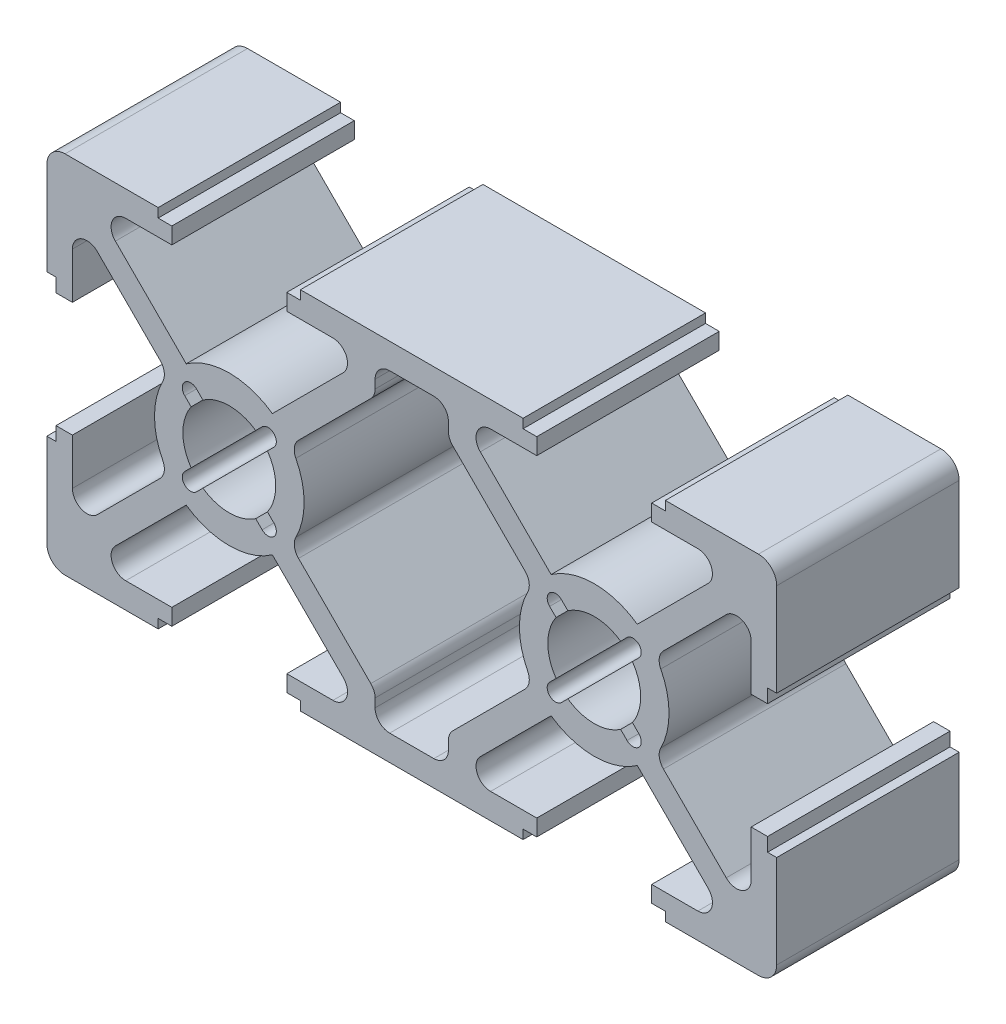
SolidWorks part; units mm, degrees
material "6063-T6"
ref_plane "Ön Düzlem" through (0, 0, 0) normal (0, 0, 1) x (1, 0, 0)
ref_plane "Üst Düzlem" through (0, 0, 0) normal (0, 1, 0) x (1, 0, 0)
ref_plane "Sağ Düzlem" through (0, 0, 0) normal (1, 0, 0) x (0, 0, -1)
sketch "Çizim3" plane through (0, 0, 0) normal (0, 0, 1) x (1, 0, 0)
  line L0 (20, 20) -> (20, 0) construction
  line L1 (0, 0) -> (40, 0) construction
  line L2 (1, 0) -> (6.1, 0)
  line L3 (0, 20) -> (40, 20) construction
  line L4 (40, 0) -> (40, 20) construction
  line L5 (26.1, 0) -> (26.1, 0.5)
  line L6 (0, 0) -> (20, 20) construction
  line L7 (20, 20) -> (40, 0) construction
  line L8 (0, 20) -> (20, 0) construction
  line L9 (20, 0) -> (40, 20) construction
  line L10 (0, 6.1) -> (0.5, 6.1)
  line L11 (0.5, 6.1) -> (0.5, 6.85)
  line L12 (0.5, 6.85) -> (1.4, 6.85)
  line L13 (1.4, 6.85) -> (1.4, 4.3213)
  line L14 (4.3213, 1.4) -> (6.85, 1.4)
  line L15 (6.85, 1.4) -> (6.85, 0.5)
  line L16 (6.85, 0.5) -> (6.1, 0.5)
  line L17 (6.1, 0.5) -> (6.1, 0)
  line L18 (0, 20) -> (0, 0) construction
  line L19 (0, 1) -> (0, 6.1)
  line L20 (6.85, 18.6) -> (6.85, 19.5)
  line L21 (6.85, 19.5) -> (6.1, 19.5)
  line L22 (1, 20) -> (6.1, 20)
  line L23 (4.3213, 18.6) -> (6.85, 18.6)
  line L24 (0, 19) -> (0, 13.9)
  line L25 (1.4, 13.15) -> (1.4, 15.6787)
  line L26 (0.5, 13.15) -> (1.4, 13.15)
  line L27 (0.5, 13.9) -> (0.5, 13.15)
  line L28 (0, 13.9) -> (0.5, 13.9)
  line L29 (6.1, 19.5) -> (6.1, 20)
  line L30 (70.8333, 107.5) -> (354.1667, 107.5) construction
  line L31 (2.7657, 16.2444) -> (6.6485, 12.3616)
  line L32 (3.7556, 17.2343) -> (7.6384, 13.3515)
  line L33 (3.7556, 2.7657) -> (7.6384, 6.6485)
  line L34 (2.7657, 3.7556) -> (6.6485, 7.6384)
  line L35 (0.495, 20.495) -> (20.495, 0.495) construction
  line L36 (-0.495, 19.505) -> (19.505, -0.495) construction
  line L37 (-0.495, 0.495) -> (19.505, 20.495) construction
  line L38 (0.495, -0.495) -> (20.495, 19.505) construction
  line L39 (26.1, 20) -> (13.9, 20)
  line L40 (13.9, 20) -> (13.9, 19.5)
  line L41 (13.9, 19.5) -> (13.15, 19.5)
  line L42 (13.15, 19.5) -> (13.15, 18.6)
  line L43 (13.15, 18.6) -> (15.6787, 18.6)
  line L44 (21.2103, 18.6) -> (18.7897, 18.6)
  line L45 (17.9897, 17.8) -> (17.9897, 17.3311)
  line L46 (26.1, 0) -> (13.9, 0)
  line L47 (13.9, 0) -> (13.9, 0.5)
  line L48 (13.9, 0.5) -> (13.15, 0.5)
  line L49 (13.15, 0.5) -> (13.15, 1.4)
  line L50 (13.15, 1.4) -> (15.6787, 1.4)
  line L51 (18.7897, 1.4) -> (21.2103, 1.4)
  line L52 (17.9897, 2.2) -> (17.9897, 2.6689)
  line L53 (8.2011, 12.4438) -> (8.5527, 12.0922)
  line L54 (7.5562, 11.7989) -> (7.9078, 11.4473)
  line L55 (12.3616, 13.3515) -> (16.2444, 17.2343)
  line L56 (13.3515, 12.3616) -> (17.7554, 16.7654)
  line L57 (7.5562, 8.2011) -> (7.9078, 8.5527)
  line L58 (8.2011, 7.5562) -> (8.5527, 7.9078)
  line L59 (12.3616, 6.6485) -> (16.2444, 2.7657)
  line L60 (13.3515, 7.6384) -> (17.7554, 3.2346)
  line L61 (26.1, 0.5) -> (26.85, 0.5)
  line L62 (12.0922, 8.5527) -> (12.4438, 8.2011)
  line L63 (11.4473, 12.0922) -> (11.7989, 12.4438)
  line L64 (12.0922, 11.4473) -> (12.4438, 11.7989)
  line L65 (11.4473, 7.9078) -> (11.7989, 7.5562)
  line L66 (26.85, 0.5) -> (26.85, 1.4)
  line L67 (26.85, 1.4) -> (24.3213, 1.4)
  line L68 (22.0103, 2.2) -> (22.0103, 2.6689)
  line L69 (26.6485, 7.6384) -> (22.2446, 3.2346)
  line L70 (27.6384, 6.6485) -> (23.7556, 2.7657)
  line L71 (36.2444, 2.7657) -> (32.3616, 6.6485)
  line L72 (37.2343, 3.7556) -> (33.3515, 7.6384)
  line L73 (35.6787, 1.4) -> (33.15, 1.4)
  line L74 (33.15, 1.4) -> (33.15, 0.5)
  line L75 (33.15, 0.5) -> (33.9, 0.5)
  line L76 (33.9, 0.5) -> (33.9, 0)
  line L77 (39, 0) -> (33.9, 0)
  line L78 (40, 1) -> (40, 6.1)
  line L79 (38.6, 6.85) -> (38.6, 4.3213)
  line L80 (39.5, 6.85) -> (38.6, 6.85)
  line L81 (39.5, 6.1) -> (39.5, 6.85)
  line L82 (40, 6.1) -> (39.5, 6.1)
  line L83 (26.1, 20) -> (26.1, 19.5)
  line L84 (26.1, 19.5) -> (26.85, 19.5)
  line L85 (26.85, 19.5) -> (26.85, 18.6)
  line L86 (26.85, 18.6) -> (24.3213, 18.6)
  line L87 (26.6485, 12.3616) -> (22.2446, 16.7654)
  line L88 (27.6384, 13.3515) -> (23.7556, 17.2343)
  line L89 (22.0103, 17.8) -> (22.0103, 17.3311)
  line L90 (27.9078, 11.4473) -> (27.5562, 11.7989)
  line L91 (27.9078, 8.5527) -> (27.5562, 8.2011)
  line L92 (28.5527, 7.9078) -> (28.2011, 7.5562)
  line L93 (31.7989, 7.5562) -> (31.4473, 7.9078)
  line L94 (32.4438, 8.2011) -> (32.0922, 8.5527)
  line L95 (32.4438, 11.7989) -> (32.0922, 11.4473)
  line L96 (31.7989, 12.4438) -> (31.4473, 12.0922)
  line L97 (36.2444, 17.2343) -> (32.3616, 13.3515)
  line L98 (35.6787, 18.6) -> (33.15, 18.6)
  line L99 (33.15, 18.6) -> (33.15, 19.5)
  line L100 (33.15, 19.5) -> (33.9, 19.5)
  line L101 (33.9, 19.5) -> (33.9, 20)
  line L102 (37.2343, 16.2444) -> (33.3515, 12.3616)
  line L103 (38.6, 13.15) -> (38.6, 15.6787)
  line L104 (39.5, 13.15) -> (38.6, 13.15)
  line L105 (39.5, 13.9) -> (39.5, 13.15)
  line L106 (40, 13.9) -> (39.5, 13.9)
  line L107 (40, 19) -> (40, 13.9)
  line L108 (39, 20) -> (33.9, 20)
  line L109 (28.5527, 12.0922) -> (28.2011, 12.4438)
  arc A0 (7.9078, 11.4473) -> (7.9078, 8.5527) centre (10, 10) ccw
  arc A1 (2.7657, 16.2444) -> (1.4, 15.6787) centre (2.2, 15.6787) ccw
  arc A2 (3.7556, 2.7657) -> (4.3213, 1.4) centre (4.3213, 2.2) ccw
  arc A3 (2.7657, 3.7556) -> (1.4, 4.3213) centre (2.2, 4.3213) cw
  arc A4 (3.7556, 17.2343) -> (4.3213, 18.6) centre (4.3213, 17.8) cw
  arc A5 (15.6787, 18.6) -> (16.2444, 17.2343) centre (15.6787, 17.8) cw
  arc A6 (18.7897, 18.6) -> (17.9897, 17.8) centre (18.7897, 17.8) ccw
  arc A7 (17.9897, 17.3311) -> (17.7554, 16.7654) centre (17.1897, 17.3311) cw
  arc A8 (15.6787, 1.4) -> (16.2444, 2.7657) centre (15.6787, 2.2) ccw
  arc A9 (18.7897, 1.4) -> (17.9897, 2.2) centre (18.7897, 2.2) cw
  arc A10 (17.9897, 2.6689) -> (17.7554, 3.2346) centre (17.1897, 2.6689) ccw
  arc A11 (6.6485, 12.3616) -> (6.6485, 7.6384) centre (10, 10) ccw
  arc A12 (12.3616, 13.3515) -> (7.6384, 13.3515) centre (10, 10) ccw
  arc A13 (7.6384, 6.6485) -> (12.3616, 6.6485) centre (10, 10) ccw
  arc A14 (13.3515, 7.6384) -> (13.3515, 12.3616) centre (10, 10) ccw
  arc A15 (11.4473, 12.0922) -> (8.5527, 12.0922) centre (10, 10) ccw
  arc A16 (8.2011, 12.4438) -> (7.5562, 11.7989) centre (7.8787, 12.1213) ccw
  arc A17 (12.4438, 11.7989) -> (11.7989, 12.4438) centre (12.1213, 12.1213) ccw
  arc A18 (11.7989, 7.5562) -> (12.4438, 8.2011) centre (12.1213, 7.8787) ccw
  arc A19 (7.5562, 8.2011) -> (8.2011, 7.5562) centre (7.8787, 7.8787) ccw
  arc A20 (8.5527, 7.9078) -> (11.4473, 7.9078) centre (10, 10) ccw
  arc A21 (12.0922, 8.5527) -> (12.0922, 11.4473) centre (10, 10) ccw
  arc A22 (21.2103, 1.4) -> (22.0103, 2.2) centre (21.2103, 2.2) ccw
  arc A23 (24.3213, 1.4) -> (23.7556, 2.7657) centre (24.3213, 2.2) cw
  arc A24 (22.0103, 2.6689) -> (22.2446, 3.2346) centre (22.8103, 2.6689) cw
  arc A25 (32.3616, 6.6485) -> (27.6384, 6.6485) centre (30, 10) cw
  arc A26 (37.2343, 3.7556) -> (38.6, 4.3213) centre (37.8, 4.3213) ccw
  arc A27 (36.2444, 2.7657) -> (35.6787, 1.4) centre (35.6787, 2.2) cw
  arc A28 (26.6485, 7.6384) -> (26.6485, 12.3616) centre (30, 10) cw
  arc A29 (21.2103, 18.6) -> (22.0103, 17.8) centre (21.2103, 17.8) cw
  arc A30 (24.3213, 18.6) -> (23.7556, 17.2343) centre (24.3213, 17.8) ccw
  arc A31 (22.0103, 17.3311) -> (22.2446, 16.7654) centre (22.8103, 17.3311) ccw
  arc A32 (28.5527, 12.0922) -> (31.4473, 12.0922) centre (30, 10) cw
  arc A33 (27.5562, 11.7989) -> (28.2011, 12.4438) centre (27.8787, 12.1213) cw
  arc A34 (27.9078, 8.5527) -> (27.9078, 11.4473) centre (30, 10) cw
  arc A35 (31.4473, 7.9078) -> (28.5527, 7.9078) centre (30, 10) cw
  arc A36 (32.4438, 8.2011) -> (31.7989, 7.5562) centre (32.1213, 7.8787) cw
  arc A37 (32.0922, 11.4473) -> (32.0922, 8.5527) centre (30, 10) cw
  arc A38 (31.7989, 12.4438) -> (32.4438, 11.7989) centre (32.1213, 12.1213) cw
  arc A39 (33.3515, 12.3616) -> (33.3515, 7.6384) centre (30, 10) cw
  arc A40 (27.6384, 13.3515) -> (32.3616, 13.3515) centre (30, 10) cw
  arc A41 (36.2444, 17.2343) -> (35.6787, 18.6) centre (35.6787, 17.8) ccw
  arc A42 (37.2343, 16.2444) -> (38.6, 15.6787) centre (37.8, 15.6787) cw
  arc A43 (39, 0) -> (40, 1) centre (39, 1) ccw
  arc A44 (40, 19) -> (39, 20) centre (39, 19) ccw
  arc A45 (0, 1) -> (1, 0) centre (1, 1) ccw
  arc A46 (0, 19) -> (1, 20) centre (1, 19) cw
  arc A48 (28.2011, 7.5562) -> (27.5562, 8.2011) centre (27.8787, 7.8787) cw
  point P10 (20, 10)
  point P109 (20, 1.4)
  point P145 (20, 18.6)
  dimension "D10" = 0.8
  dimension "D11" = 0.8
  dimension "D13" = 0.8
  dimension "D14" = 0.8
  dimension "D16" = 0.8
  dimension "D17" = 0.8
  dimension "D18" = 20
  dimension "D20" = 1
  dimension "D1" = 6.3
  dimension "D2" = 20
  dimension "D3" = 6.1
  dimension "D4" = 0.5
  dimension "D5" = 1.4
  dimension "D6" = 0.7
  dimension "D12" = 6.3
  dimension "D15" = 6.3
  dimension "D19" = 10
  dimension "D7" = 0.7
  dimension "D8" = 0.7
  dimension "D9" = 0.7
extrude "Yükseklik-Ekstrüzyon2" add sketch "Çizim3" along normal blind 10 contours L22 L29 L21 L20 L23 A4 L32 A12 L55 A5 L43 L42 L41 L40 L39 L83 L84 L85 L86 A30 L88 A40 L97 A41 L98 L99 L100 L101 L108 A44 L107 L106 L105 L104 L103 A42 L102 A39 L72 A26 L79 L80 L81 L82 L78 A43 L77 L76 L75 L74 L73 A27 L71 A25 L70 A23 L67 L66 L61 L5 L46 L47 L48 L49 L50 A8 L59 A13 L33 A2 L14 L15 L16 L17 L2 A45 L19 L10 L11 L12 L13 A3 L34 A11 L31 A1 L25 L26 L27 L28 L24 A46
fillet "Radyus1" radius 0.8 8 edges at (26.6485, 7.6384, 5) (26.6485, 12.3616, 5) (33.3515, 7.6384, 5) (33.3515, 12.3616, 5) (13.3515, 12.3616, 5) (13.3515, 7.6384, 5) (6.6485, 7.6384, 5) (6.6485, 12.3616, 5)
